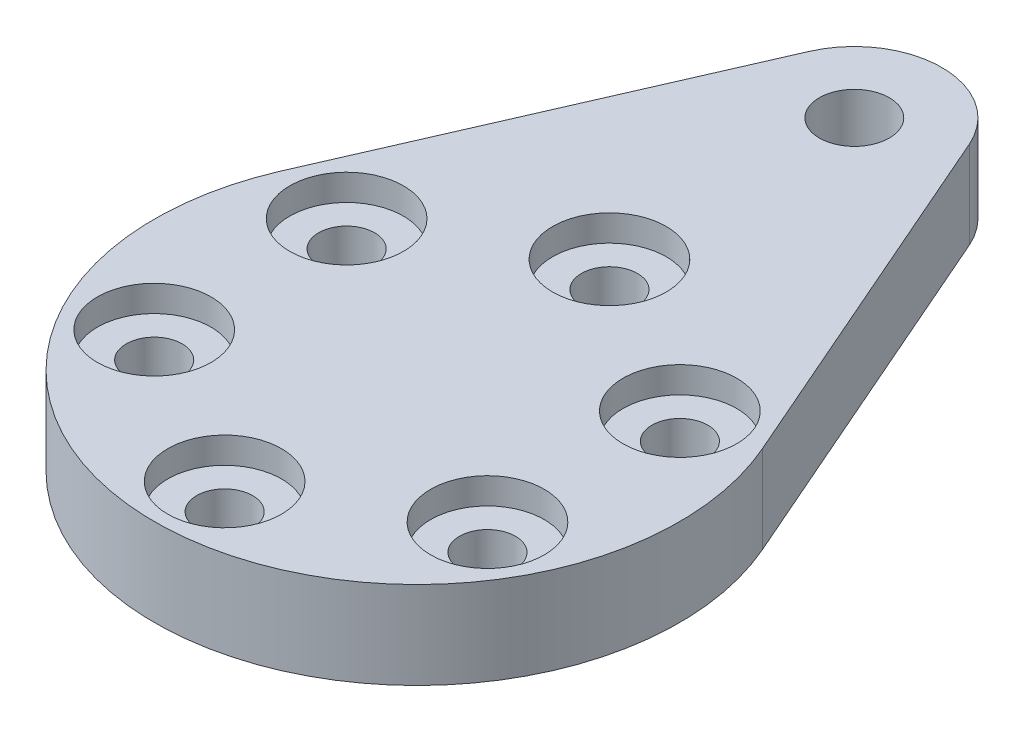
SolidWorks part; units mm, degrees
ref_plane "Front Plane" through (0, 0, 0) normal (0, 0, 1) x (1, 0, 0)
ref_plane "Top Plane" through (0, 0, 0) normal (0, 1, 0) x (1, 0, 0)
ref_plane "Right Plane" through (0, 0, 0) normal (1, 0, 0) x (0, 0, -1)
sketch "Sketch4" plane through (0, 0, 0) normal (0, 1, 0) x (1, 0, 0)
  line L0 (0, 0) -> (0, 25) construction
  line L1 (-4.5826, 27) -> (-13.7477, 6)
  line L2 (4.5826, 27) -> (13.7477, 6)
  circle A0 centre (0, 0) radius 11 construction
  circle A1 centre (0, 0) radius 15
  circle A2 centre (0, 11) radius 1.6
  circle A3 centre (9.5263, 5.5) radius 1.6
  circle A4 centre (9.5263, -5.5) radius 1.6
  circle A5 centre (0, -11) radius 1.6
  circle A6 centre (-9.5263, -5.5) radius 1.6
  circle A7 centre (-9.5263, 5.5) radius 1.6
  circle A8 centre (0, 25) radius 2
  circle A9 centre (0, 25) radius 5
  point P18 (0, 0)
  dimension "D1" = 22
  dimension "D2" = 30
  dimension "D3" = 3.2
  dimension "D6" = 4
  dimension "D7" = 10
  dimension "D5" = 25
  dimension "D4" = 6
extrude "Boss-Extrude1" add sketch "Sketch4" along normal blind 5 contours A9 A8 | A9 L1 A1 | A9 A1 L2 | A1 A7 A6 A5 A4 A3 A2
sketch "Sketch6" plane through (0, 5, 0) normal (0, 1, 0) x (1, 0, 0)
  circle A0 centre (0, 0) radius 11 construction
  circle A1 centre (0, 11) radius 3.25
  circle A2 centre (9.5263, 5.5) radius 3.25
  circle A3 centre (9.5263, -5.5) radius 3.25
  circle A4 centre (0, -11) radius 3.25
  circle A5 centre (-9.5263, -5.5) radius 3.25
  circle A6 centre (-9.5263, 5.5) radius 3.25
  point P19 (0, 0)
  dimension "D1" = 6.5
  dimension "D3" = 22
  dimension "D2" = 6
extrude "Cut-Extrude1" cut sketch "Sketch6" against normal blind 1.5
